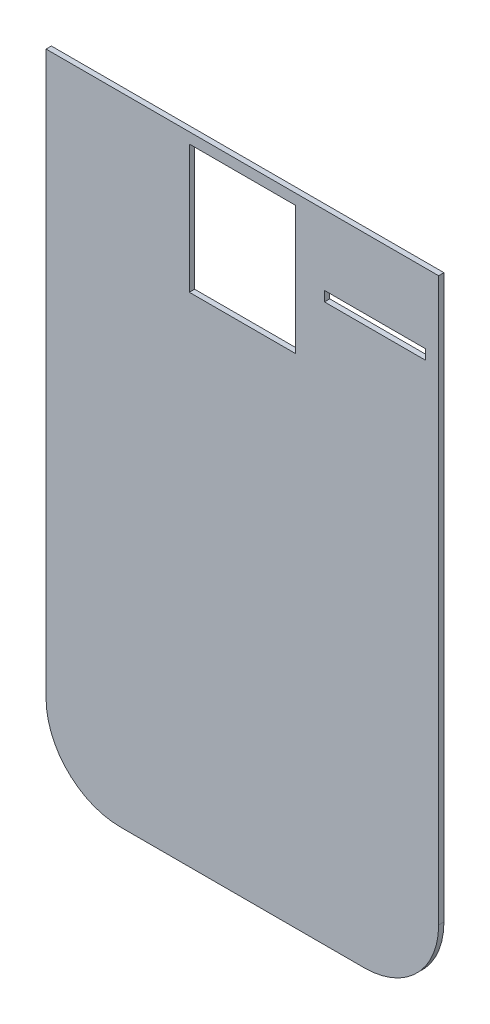
SolidWorks part; units mm, degrees
ref_plane "Front Plane" through (0, 0, 0) normal (0, 0, 1) x (1, 0, 0)
ref_plane "Top Plane" through (0, 0, 0) normal (0, 1, 0) x (1, 0, 0)
ref_plane "Right Plane" through (0, 0, 0) normal (1, 0, 0) x (0, 0, -1)
sketch "Sketch1" plane through (0, 0, 0) normal (1, 0, 0) x (0, 0, -1)
  line L0 (0, 0) -> (-350, 0)
  line L1 (-350, 0) -> (-350, 860)
  line L2 (-310, 900) -> (-158.4889, 900)
  line L3 (-158.4889, 900) -> (-158.4889, 1060.6969)
  line L4 (0, 900) -> (0, 0)
  line L5 (-158.4889, 1060.6969) -> (-350, 900) construction
  arc A0 (0, 900) -> (-158.4889, 1060.6969) centre (-160.7123, 900) ccw
  arc A1 (-350, 860) -> (-310, 900) centre (-310, 860) cw
  dimension "D5" = 40
  dimension "D1" = 900
  dimension "D2" = 350
  dimension "D3" = 250
  dimension "D4" = 40
extrude "Boss-Extrude1" add sketch "Sketch1" along normal blind 400
sketch "Sketch2" plane through (0, 0, 350) normal (0, 0, 1) x (1, 0, 0)
  line L0 (200, 850) -> (200, 900) construction
  line L1 (150, 850) -> (250, 850)
  line L2 (150, 850) -> (150, 729)
  line L3 (150, 729) -> (250, 729)
  line L4 (250, 850) -> (250, 729)
  line L5 (400, 900) -> (0, 900) construction
  line L6 (277.35, 789.5) -> (250, 789.5) construction
  line L7 (372.65, 794.2) -> (277.35, 794.2)
  line L8 (372.65, 794.2) -> (372.65, 784.8)
  line L9 (372.65, 784.8) -> (277.35, 784.8)
  line L10 (277.35, 794.2) -> (277.35, 784.8)
  line L11 (250, 850) -> (400, 850) construction
  line L12 (400, 860) -> (400, 0) construction
  line L13 (325, 850) -> (325, 794.2) construction
  dimension "D1" = 121
  dimension "D2" = 100
  dimension "D3" = 50
  dimension "D4" = 9.4
  dimension "D5" = 95.3
extrude "Cut-Extrude1" cut sketch "Sketch2" against normal blind 268
sketch "Sketch3" plane through (0, 0, 0) normal (-1, 0, 0) x (0, 0, 1)
  line L0 (350, 860) -> (345, 860)
  line L1 (345, 860) -> (345, -140.2682)
  line L2 (345, -140.2682) -> (-654.0486, 0)
  line L3 (-654.0486, 0) -> (-155.3829, 1729.3232)
  line L4 (-155.3829, 1729.3232) -> (878.3154, 1431.2471)
  line L5 (878.3154, 1431.2471) -> (350, 860)
  dimension "D1" = 5
extrude "Cut-Extrude2" cut sketch "Sketch3" against normal blind 574
sketch "Sketch4" plane through (0, 0, 350) normal (0, 0, 1) x (1, 0, 0)
  line L0 (15, 917.9715) -> (15, 330)
  line L2 (85, 260) -> (315, 260)
  line L4 (385, 330) -> (385, 917.9715)
  line L5 (385, 917.9715) -> (580.5406, 679.2265)
  line L6 (580.5406, 679.2265) -> (899.5487, -163.8862)
  line L7 (899.5487, -163.8862) -> (163.4837, -163.8862)
  line L8 (163.4837, -163.8862) -> (110.9076, -163.8862)
  line L9 (-601.6488, 753.8124) -> (15, 917.9715)
  line L10 (-601.6488, 753.8124) -> (110.9076, -163.8862)
  line L11 (400, 860) -> (0, 860) construction
  line L12 (385, 917.9715) -> (15, 917.9715) construction
  line L13 (200, 860) -> (200, 917.9715) construction
  line L14 (400, 860) -> (400, 0) construction
  arc A0 (15, 330) -> (85, 260) centre (85, 330) ccw
  arc A1 (315, 260) -> (385, 330) centre (315, 330) ccw
  dimension "D3" = 70
  dimension "D1" = 600
  dimension "D2" = 15
extrude "Cut-Extrude3" cut sketch "Sketch4" against normal blind 574
